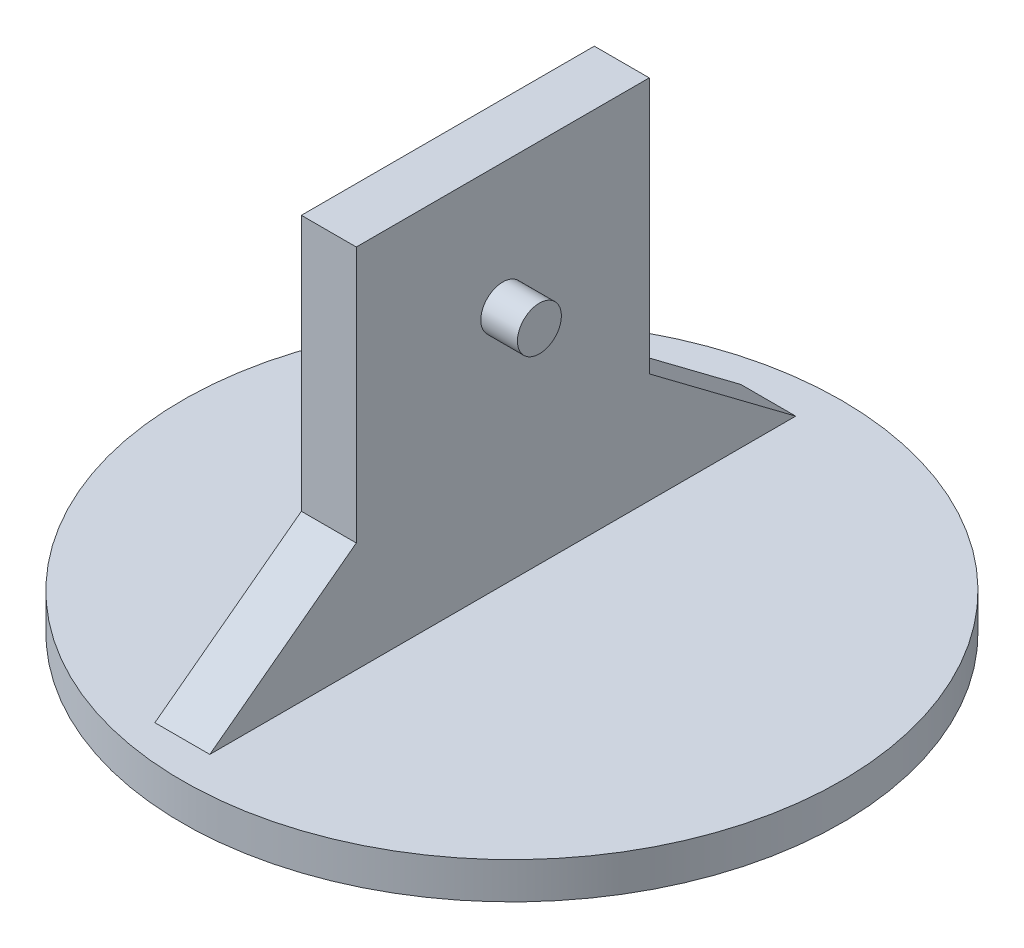
SolidWorks part; units mm, degrees
ref_plane "Front Plane" through (0, 0, 0) normal (0, 0, 1) x (1, 0, 0)
ref_plane "Top Plane" through (0, 0, 0) normal (0, 1, 0) x (1, 0, 0)
ref_plane "Right Plane" through (0, 0, 0) normal (1, 0, 0) x (0, 0, -1)
sketch "Sketch1" plane through (0, 0, 0) normal (1, 0, 0) x (0, 0, -1)
  line L5 (-40, -50) -> (-80, -50)
  line L6 (-40, 50) -> (40, 50)
  line L12 (-40, 50) -> (-40, -50)
  line L13 (-40, -50) -> (40, -50)
  line L14 (40, 50) -> (40, -50)
  line L15 (-40, 50) -> (40, -50) construction
  line L16 (-40, -50) -> (40, 50) construction
  line L17 (-80, -50) -> (-40, -20)
  line L18 (-40, -20) -> (-40, -50)
  line L19 (0, 0) -> (0, -40.179) construction
  line L25 (40, -50) -> (40, -20)
  line L26 (40, -50) -> (80, -50)
  line L27 (80, -50) -> (40, -20)
  point P0 (0, 0)
  dimension "D1" = 80
  dimension "D2" = 40
  dimension "100" = 100
  dimension "D3" = 30
  dimension "D4" = 40
extrude "Boss-Extrude1" add sketch "Sketch1" along normal blind 15 contours L26 L27 L14 | L14 L6 L12 L13 | L17 L5 L12
sketch "Sketch2" plane through (15, 0, 0) normal (1, 0, 0) x (0, 0, -1)
  line L0 (0, 0) -> (0, 15.7289) construction
  circle A0 centre (0, 15.7289) radius 6
  dimension "D1" = 12
sketch "Sketch3" plane through (0, -50, 0) normal (0, -1, 0) x (1, 0, 0)
  line L0 (0, 0) -> (7.5, 0) construction
  line L1 (7.5, 0) -> (17.5, 0) construction
  circle A0 centre (17.5, 0) radius 90
  dimension "D3" = 180
  dimension "D1" = 7.5
  dimension "D2" = 10
extrude "Boss-Extrude2" add sketch "Sketch3" along normal blind 10
extrude "Boss-Extrude3" add sketch "Sketch2" along normal blind 10
sketch "Sketch4" plane through (0, -60, 0) normal (0, -1, 0) x (1, 0, 0)
  line L0 (-72.5, 0) -> (17.5, 0) construction
  circle A0 centre (17.5, 0) radius 90 construction
  circle A1 centre (17.5, 0) radius 5
  dimension "D1" = 10
extrude "Boss-Extrude4" add sketch "Sketch4" along normal blind 10
